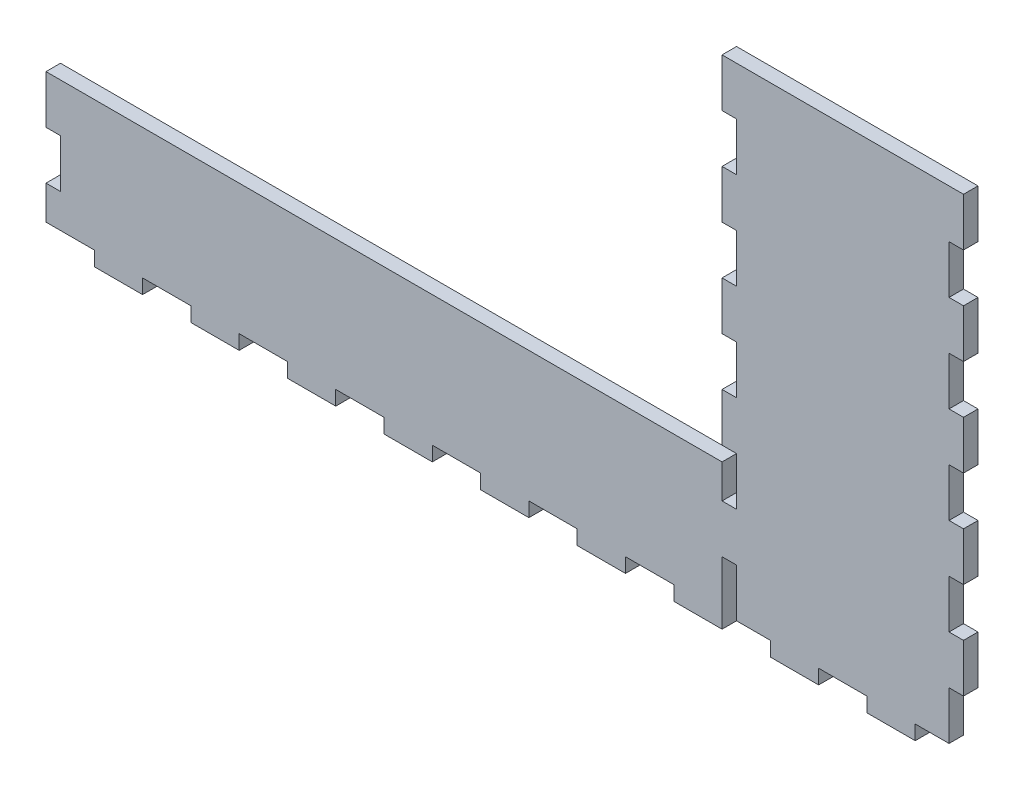
SolidWorks part; units mm, degrees
ref_plane "Front Plane" through (0, 0, 0) normal (0, 0, 1) x (1, 0, 0)
ref_plane "Top Plane" through (0, 0, 0) normal (0, 1, 0) x (1, 0, 0)
ref_plane "Right Plane" through (0, 0, 0) normal (1, 0, 0) x (0, 0, -1)
sketch "Sketch1" plane through (0, 0, 0) normal (0, 0, 1) x (1, 0, 0)
  line L1 (-220.2312, -93.9017) -> (59.7688, -93.9017)
  line L2 (-220.2312, -93.9017) -> (-220.2312, -153.9017)
  line L3 (-220.2312, -153.9017) -> (59.7688, -153.9017)
  line L4 (59.7688, -93.9017) -> (59.7688, 52.0983)
  line L5 (59.7688, -153.9017) -> (159.7688, -153.9017)
  line L7 (59.7688, 52.0983) -> (159.7688, 52.0983)
  line L8 (159.7688, -153.9017) -> (159.7688, 52.0983)
  dimension "D1" = 60
  dimension "D2" = 280
  dimension "D3" = 100
  dimension "D4" = 206
  dimension "D5" = 100
extrude "Boss-Extrude1" add sketch "Sketch1" along normal blind 6
sketch "Sketch2" plane through (0, 0, 6) normal (0, 0, 1) x (1, 0, 0)
  line L0 (-220.2312, -153.9017) -> (159.7688, -153.9017) construction
  line L1 (-220.2312, -147.9017) -> (-200.2312, -147.9017)
  line L2 (-220.2312, -147.9017) -> (-220.2312, -153.9017)
  line L3 (-220.2312, -153.9017) -> (-200.2312, -153.9017)
  line L4 (-200.2312, -147.9017) -> (-200.2312, -153.9017)
  line L5 (-220.2312, -93.9017) -> (-220.2312, -153.9017) construction
  dimension "D1" = 0
  dimension "D2" = 20
  dimension "D3" = 6
extrude "Cut-Extrude1" cut sketch "Sketch2" against normal blind 10
pattern_linear "LPattern1" count 10 spacing 40 along (1, 0, 0) of "Cut-Extrude1"
sketch "Sketch3" plane through (0, 0, 6) normal (0, 0, 1) x (1, 0, 0)
  line L0 (-220.2312, -93.9017) -> (-220.2312, -147.9017) construction
  line L1 (-220.2312, -113.9017) -> (-214.2312, -113.9017)
  line L2 (-220.2312, -113.9017) -> (-220.2312, -133.9017)
  line L3 (-220.2312, -133.9017) -> (-214.2312, -133.9017)
  line L4 (-214.2312, -113.9017) -> (-214.2312, -133.9017)
  line L6 (-200.2312, -153.9017) -> (-180.2312, -153.9017) construction
  dimension "D1" = 20
  dimension "D2" = 6
  dimension "D3" = 20
extrude "Cut-Extrude2" cut sketch "Sketch3" against normal blind 10
sketch "Sketch4" plane through (0, 0, 6) normal (0, 0, 1) x (1, 0, 0)
  line L0 (159.7688, -147.9017) -> (159.7688, 52.0983) construction
  line L1 (159.7688, 32.0983) -> (153.7688, 32.0983)
  line L2 (159.7688, 32.0983) -> (159.7688, 12.0983)
  line L3 (159.7688, 12.0983) -> (153.7688, 12.0983)
  line L4 (153.7688, 32.0983) -> (153.7688, 12.0983)
  line L5 (159.7688, 52.0983) -> (59.7688, 52.0983) construction
  dimension "D1" = 6
  dimension "D2" = 20
  dimension "D3" = 20
extrude "Cut-Extrude3" cut sketch "Sketch4" against normal blind 10
pattern_linear "LPattern2" count 5 spacing 40 along (0, -1, 0) of "Cut-Extrude3"
sketch "Sketch5" plane through (0, 0, 6) normal (0, 0, 1) x (1, 0, 0)
  line L0 (59.7688, 52.0983) -> (59.7688, -93.9017) construction
  line L1 (59.7688, 32.0983) -> (65.7688, 32.0983)
  line L2 (59.7688, 32.0983) -> (59.7688, 12.0983)
  line L3 (59.7688, 12.0983) -> (65.7688, 12.0983)
  line L4 (65.7688, 32.0983) -> (65.7688, 12.0983)
  line L5 (159.7688, 32.0983) -> (153.7688, 32.0983) construction
  dimension "D1" = 20
  dimension "D2" = 0
  dimension "D3" = 6
extrude "Cut-Extrude4" cut sketch "Sketch5" against normal blind 10
pattern_linear "LPattern3" count 5 spacing 40 along (0, -1, 0) of "Cut-Extrude4"
